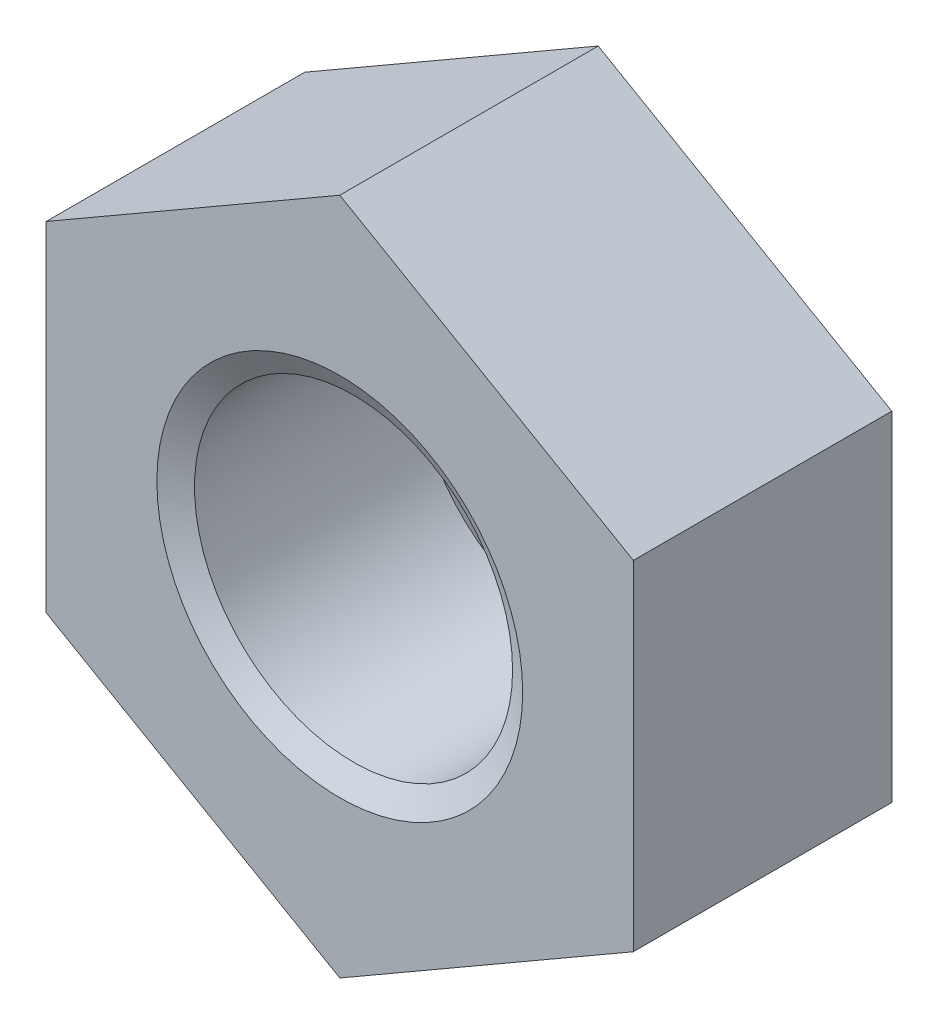
SolidWorks part; units mm, degrees
material "AISI 1020"
ref_plane "Спереди" through (0, 0, 0) normal (0, 0, 1) x (1, 0, 0)
ref_plane "Сверху" through (0, 0, 0) normal (0, 1, 0) x (1, 0, 0)
ref_plane "Справа" through (0, 0, 0) normal (1, 0, 0) x (0, 0, -1)
sketch "Эскиз1" plane through (0, 0, 0) normal (0, 0, 1) x (1, 0, 0)
  line L1 (0, 1.705) -> (-1.4766, 0.8525)
  line L2 (-1.4766, 0.8525) -> (-1.4766, -0.8525)
  line L3 (-1.4766, -0.8525) -> (0, -1.705)
  line L4 (0, -1.705) -> (1.4766, -0.8525)
  line L5 (1.4766, -0.8525) -> (1.4766, 0.8525)
  line L6 (1.4766, 0.8525) -> (0, 1.705)
  circle A0 centre (0, 0) radius 1.705 construction
  circle A1 centre (0, 0) radius 0.8
  dimension "D1" = 3.41
  dimension "D2" = 1.6
extrude "Бобышка-Вытянуть1" add sketch "Эскиз1" along normal blind 1.3
chamfer "Фаска1" distance 0.12 angle 30 2 edges at (0.8, 0, 0) (0.8, 0, 1.3)
